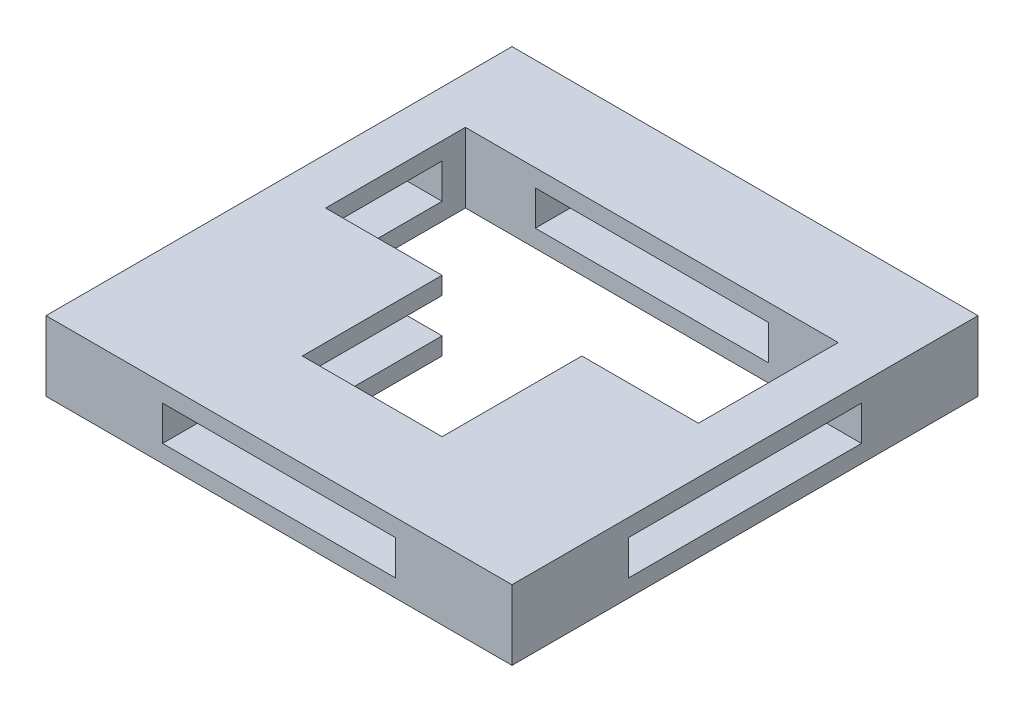
SolidWorks part; units mm, degrees
ref_plane "Front Plane" through (0, 0, 0) normal (0, 0, 1) x (1, 0, 0)
ref_plane "Top Plane" through (0, 0, 0) normal (0, 1, 0) x (1, 0, 0)
ref_plane "Right Plane" through (0, 0, 0) normal (1, 0, 0) x (0, 0, -1)
sketch "Sketch1" plane through (0, 0, 0) normal (0, 1, 0) x (1, 0, 0)
  line L1 (10, -10) -> (-10, -10)
  line L2 (10, -10) -> (10, 10)
  line L3 (10, 10) -> (-10, 10)
  line L4 (-10, -10) -> (-10, 10)
  line L5 (8, -8) -> (-8, -8) construction
  line L6 (8, -8) -> (8, 8) construction
  line L7 (8, 8) -> (-8, 8) construction
  line L8 (-8, -8) -> (-8, 8) construction
  line L9 (0, 8) -> (0, -8) construction
  line L10 (8, 0) -> (-8, 0) construction
  line L11 (-8, 0) -> (8, 0)
  line L12 (-8, 0) -> (-8, 6)
  line L13 (-8, 6) -> (8, 6)
  line L14 (8, 0) -> (8, 6)
  line L15 (3, 0) -> (-3, 0)
  line L16 (3, 0) -> (3, -6)
  line L17 (3, -6) -> (-3, -6)
  line L18 (-3, 0) -> (-3, -6)
  point P0 (0, 0)
  point P4 (0, 0)
  dimension "D1" = 20
  dimension "D2" = 20
  dimension "D3" = 16
  dimension "D4" = 16
  dimension "D5" = 6
  dimension "D6" = 6
  dimension "D7" = 6
  dimension "D8" = 3
extrude "Boss-Extrude1" add sketch "Sketch1" along normal blind 3 contours L4 L1 L2 L3 L18 L11 L12 L13 L14 L16 L17
sketch "Sketch2" plane through (0, 0, 10) normal (0, 0, 1) x (1, 0, 0)
  line L0 (10, 0) -> (-10, 0) construction
  line L1 (5, 0.75) -> (-5, 0.75)
  line L2 (5, 0.75) -> (5, 2.25)
  line L3 (5, 2.25) -> (-5, 2.25)
  line L4 (-5, 0.75) -> (-5, 2.25)
  line L5 (0, 2.25) -> (0, 0.75) construction
  line L6 (5, 1.5) -> (-5, 1.5) construction
  line L7 (-10, 3) -> (-10, 0) construction
  point P0 (0, 1.5)
  point P8 (-10, 1.5)
  dimension "D1" = 10
  dimension "D2" = 1.5
  dimension "D3" = 0.75
  dimension "D4" = 5
extrude "Cut-Extrude1" cut sketch "Sketch2" against normal through all
sketch "Sketch3" plane through (10, 0, 0) normal (1, 0, 0) x (0, 0, -1)
  line L0 (-10, 3) -> (10, 3) construction
  line L1 (5, 0.75) -> (-5, 0.75)
  line L2 (5, 0.75) -> (5, 2.25)
  line L3 (5, 2.25) -> (-5, 2.25)
  line L4 (-5, 0.75) -> (-5, 2.25)
  line L5 (0, 2.25) -> (0, 0.75) construction
  line L6 (5, 1.5) -> (-5, 1.5) construction
  line L8 (-10, 3) -> (-10, 0) construction
  point P0 (0, 1.5)
  dimension "D1" = 0.75
  dimension "D2" = 10
  dimension "D3" = 1.5
  dimension "D4" = 5
extrude "Cut-Extrude2" cut sketch "Sketch3" against normal through all
